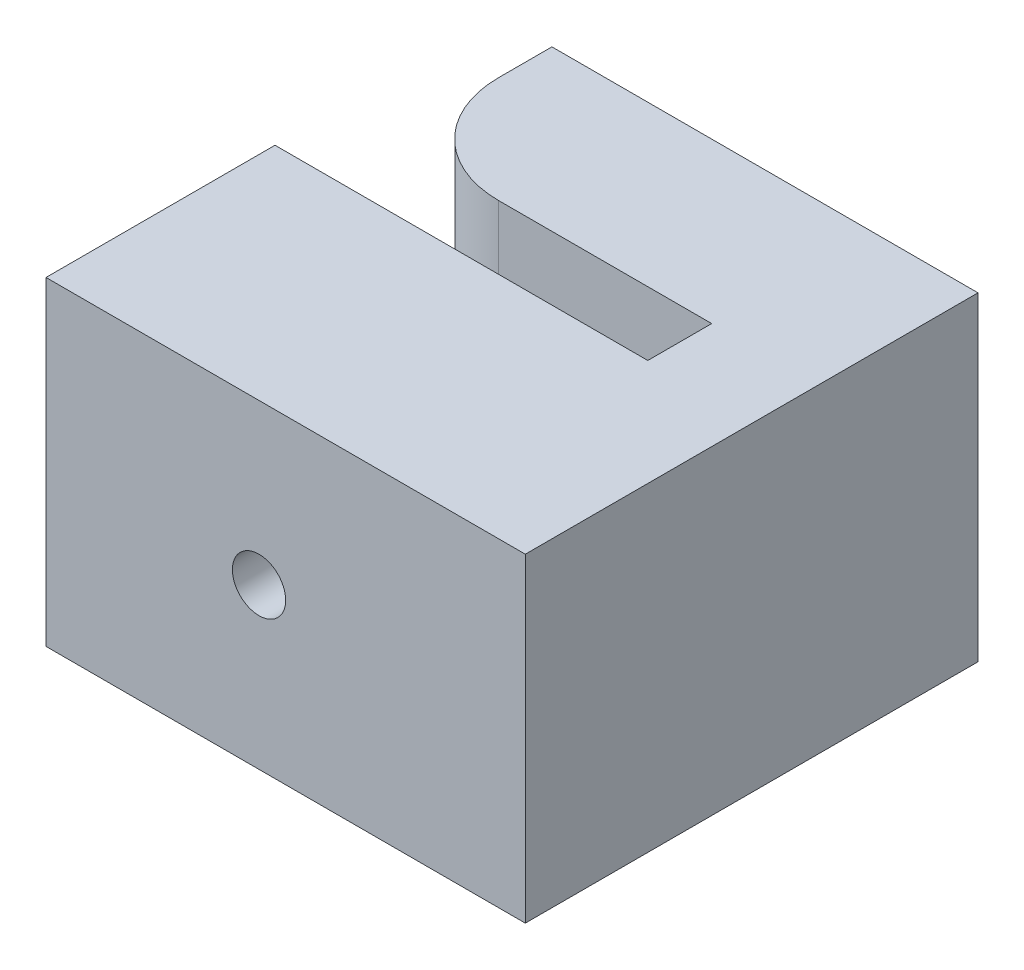
SolidWorks part; units mm, degrees
ref_plane "Plan de face" through (0, 0, 0) normal (0, 0, 1) x (1, 0, 0)
ref_plane "Plan de dessus" through (0, 0, 0) normal (0, 1, 0) x (1, 0, 0)
ref_plane "Plan de droite" through (0, 0, 0) normal (1, 0, 0) x (0, 0, -1)
sketch "Esquisse2" plane through (0, 0, 0) normal (0, 1, 0) x (1, 0, 0)
  line L0 (-4, 1.25) -> (-4, 4.25)
  line L1 (-4, -4.25) -> (4, -4.25)
  line L3 (-4, 4.25) -> (4, 4.25)
  line L4 (4, -4.25) -> (4, 4.25)
  line L5 (-4, -4.25) -> (4, 4.25) construction
  line L6 (-4, 4.25) -> (4, -4.25) construction
  line L7 (-4, 1.25) -> (2, 1.25)
  line L9 (-4, 0.05) -> (2, 0.05)
  line L10 (2, 1.25) -> (2, 0.05)
  line L11 (-4, 4.25) -> (-4, -4.25) construction
  line L12 (-4, 0.05) -> (-5, 0.05)
  line L14 (-4, -4.25) -> (-5, -4.25)
  line L15 (-5, 0.05) -> (-5, -4.25)
  point P1 (0, 0)
  dimension "D1" = 6
  dimension "D2" = 2
  dimension "D3" = 3
  dimension "D4" = 4.3
  dimension "D5" = 1.2
  dimension "D6" = 1
extrude "Boss.-Extru.1" add sketch "Esquisse2" along normal mid plane 6
sketch "Esquisse3" plane through (0, 0, -4.25) normal (0, 0, -1) x (-1, 0, 0)
  line L5 (4.4, 0) -> (-4.4, 0) construction
  line L6 (-2, 3) -> (-2, -3) construction
  line L7 (-2, 3) -> (-2, -3) construction
  circle A1 centre (1, 0) radius 0.5
  dimension "D1" = 3
  dimension "D2" = 1
extrude "Enlèv. mat.-Extru.1" cut sketch "Esquisse3" against normal through all
fillet "Congé1" radius 2 1 edges at (-4, 0, -1.25)
